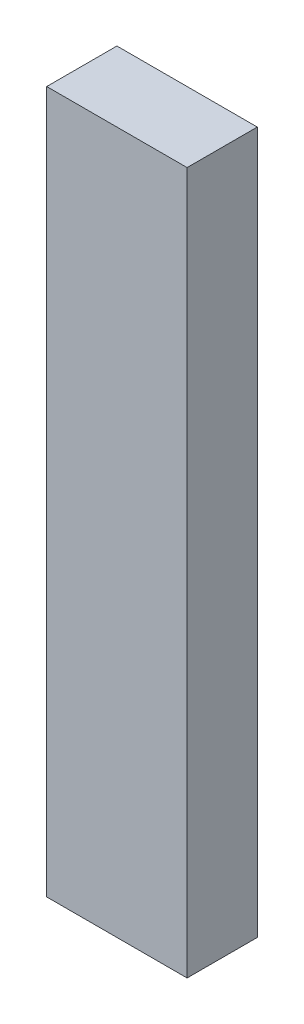
SolidWorks part; units mm, degrees
ref_plane "Front Plane" through (0, 0, 0) normal (0, 0, 1) x (1, 0, 0)
ref_plane "Top Plane" through (0, 0, 0) normal (0, 1, 0) x (1, 0, 0)
ref_plane "Right Plane" through (0, 0, 0) normal (1, 0, 0) x (0, 0, -1)
sketch "Sketch1" plane through (0, 0, 0) normal (0, 0, 1) x (1, 0, 0)
  line L1 (0, 0) -> (4, 0)
  line L2 (0, 0) -> (0, 20)
  line L3 (0, 20) -> (4, 20)
  line L4 (4, 0) -> (4, 20)
  dimension "D1" = 20
  dimension "D2" = 4
extrude "Boss-Extrude1" add sketch "Sketch1" along normal blind 2
